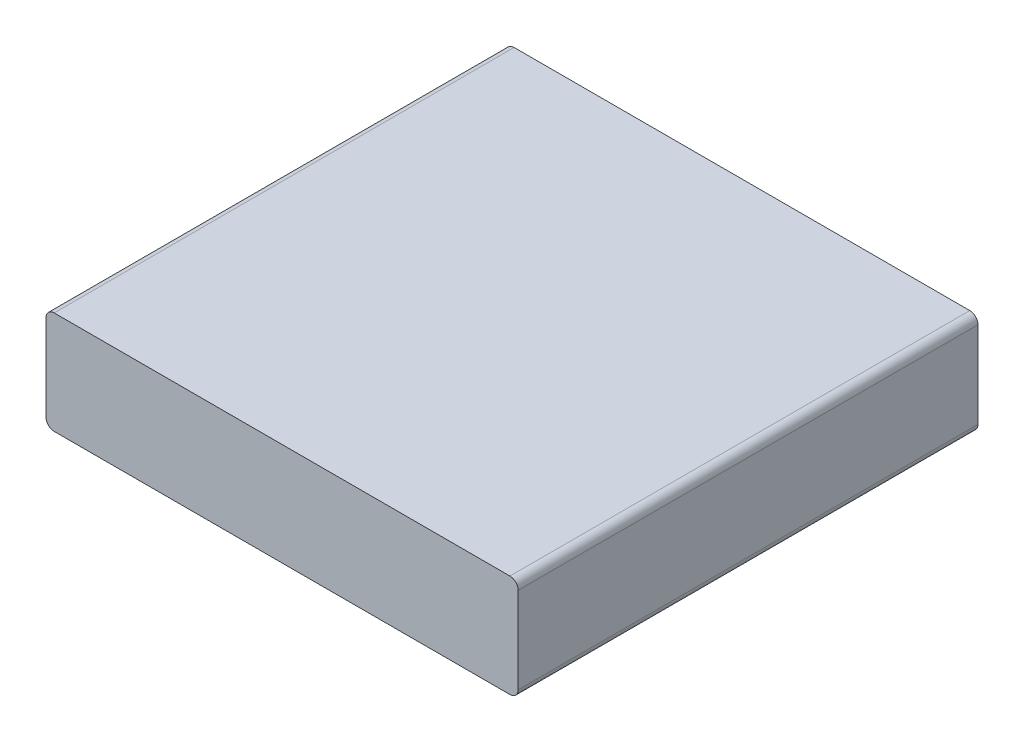
SolidWorks part; units mm, degrees
material "Polyurethane Foam Rigid"
ref_plane "Front Plane" through (0, 0, 0) normal (0, 0, 1) x (1, 0, 0)
ref_plane "Top Plane" through (0, 0, 0) normal (0, 1, 0) x (1, 0, 0)
ref_plane "Right Plane" through (0, 0, 0) normal (1, 0, 0) x (0, 0, -1)
sketch "Sketch1" plane through (0, 0, 0) normal (0, 0, 1) x (1, 0, 0)
  line L1 (-29.3403, 15.8854) -> (85.6597, 15.8854)
  line L2 (-29.3403, 15.8854) -> (-29.3403, -9.1146)
  line L3 (-29.3403, -9.1146) -> (85.6597, -9.1146)
  line L4 (85.6597, 15.8854) -> (85.6597, -9.1146)
  dimension "D1" = 25
  dimension "D2" = 115
extrude "Boss-Extrude1" add sketch "Sketch1" against normal blind 112
fillet "Fillet1" radius 2 4 edges at (85.6597, -9.1146, -56) (85.6597, 15.8854, -56) (-29.3403, -9.1146, -56) (-29.3403, 15.8854, -56)
